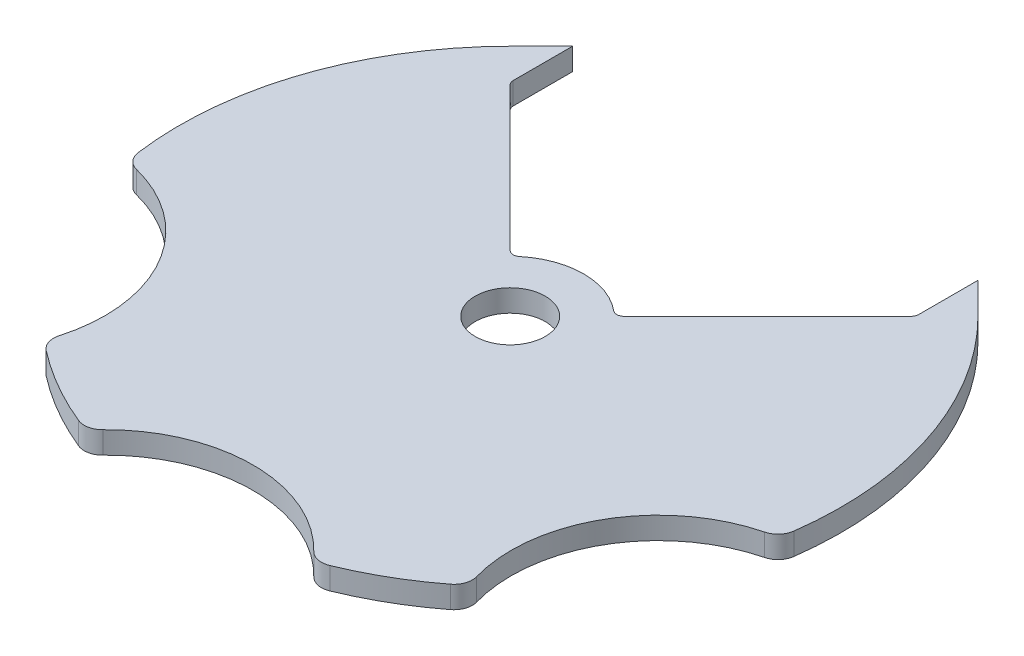
SolidWorks part; units mm, degrees
material "ABS"
ref_plane "Front Plane" through (0, 0, 0) normal (0, 0, 1) x (1, 0, 0)
ref_plane "Top Plane" through (0, 0, 0) normal (0, 1, 0) x (1, 0, 0)
ref_plane "Right Plane" through (0, 0, 0) normal (1, 0, 0) x (0, 0, -1)
sketch "Sketch1" plane through (0, 0, 0) normal (0, 1, 0) x (1, 0, 0)
  line L0 (-31.8198, 31.8198) -> (-7.0711, 7.0711)
  line L1 (7.0711, 7.0711) -> (31.8198, 31.8198)
  line L2 (0, 0) -> (0, 20) construction
  line L3 (0, 0) -> (-7.0711, 7.0711) construction
  line L4 (7.0711, 7.0711) -> (0, 0) construction
  arc A0 (-31.8198, 31.8198) -> (31.8198, 31.8198) centre (0, 0) ccw
  circle A1 centre (0, 0) radius 4.7625
  arc A2 (7.0711, 7.0711) -> (-7.0711, 7.0711) centre (0, 0) ccw
  dimension "D1" = 9.525
  dimension "D2" = 90
  dimension "D3" = 20
  dimension "D4" = 45
extrude "Boss-Extrude1" add sketch "Sketch1" along normal blind 3
sketch "Sketch2" plane through (0, 3, 0) normal (0, 1, 0) x (1, 0, 0)
  line L0 (4.0536, 2.5) -> (4.0536, -2.5)
  arc A0 (4.0536, -2.5) -> (4.0536, 2.5) centre (0, 0) ccw
  circle A1 centre (0, 0) radius 4.7625 construction
  dimension "D1" = 5
extrude "Shaft D" [suppressed] add sketch "Sketch2" against normal up to surface (10 mm away)
sketch "Sketch3" plane through (0, 3, 0) normal (0, 1, 0) x (1, 0, 0)
  line L0 (-31.8198, 31.8198) -> (-27.5772, 36.0624)
  line L1 (-27.5772, 36.0624) -> (-27.5772, 27.5772)
  line L2 (-7.0711, 7.0711) -> (-31.8198, 31.8198) construction
  line L3 (-27.5772, 27.5772) -> (-31.8198, 31.8198)
  line L4 (0, 0) -> (0, 30.6174) construction
  line L5 (27.5772, 27.5772) -> (31.8198, 31.8198)
  line L6 (27.5772, 36.0624) -> (27.5772, 27.5772)
  line L7 (31.8198, 31.8198) -> (27.5772, 36.0624)
  dimension "D1" = 6
extrude "Boss-Extrude2" add sketch "Sketch3" against normal up to surface (3 mm away) up to face at (0, 0, -0.9727)
fillet "Fillet1" radius 1 4 edges at (7.0711, 1.5, -7.0711) (-7.0711, 1.5, -7.0711) (27.5772, 1.5, -27.5772) (-27.5772, 1.5, -27.5772)
sketch "Sketch4" plane through (0, 3, 0) normal (0, 1, 0) x (1, 0, 0)
  line L0 (-47.6314, -27.5) -> (47.6314, -27.5) construction
  line L1 (47.6314, -27.5) -> (0, -55) construction
  line L2 (0, -55) -> (-47.6314, -27.5) construction
  line L3 (-47.6314, -27.5) -> (0, 0) construction
  line L4 (0, 0) -> (0, -55) construction
  line L5 (0, 0) -> (47.6314, -27.5) construction
  circle A0 centre (-47.6314, -27.5) radius 20
  circle A1 centre (47.6314, -27.5) radius 20
  circle A2 centre (0, -55) radius 20
  point P6 (0, -27.5)
  dimension "D1" = 40
  dimension "D2" = 60
  dimension "D3" = 55
extrude "Cut-Extrude1" cut sketch "Sketch4" against normal blind 10
fillet "Fillet2" radius 2.5 6 edges at (44.3231, 1.5, 7.7755) (28.8954, 1.5, 34.4972) (15.4278, 1.5, 42.2727) (-15.4278, 1.5, 42.2727) (-28.8954, 1.5, 34.4972) (-44.3231, 1.5, 7.7755)
